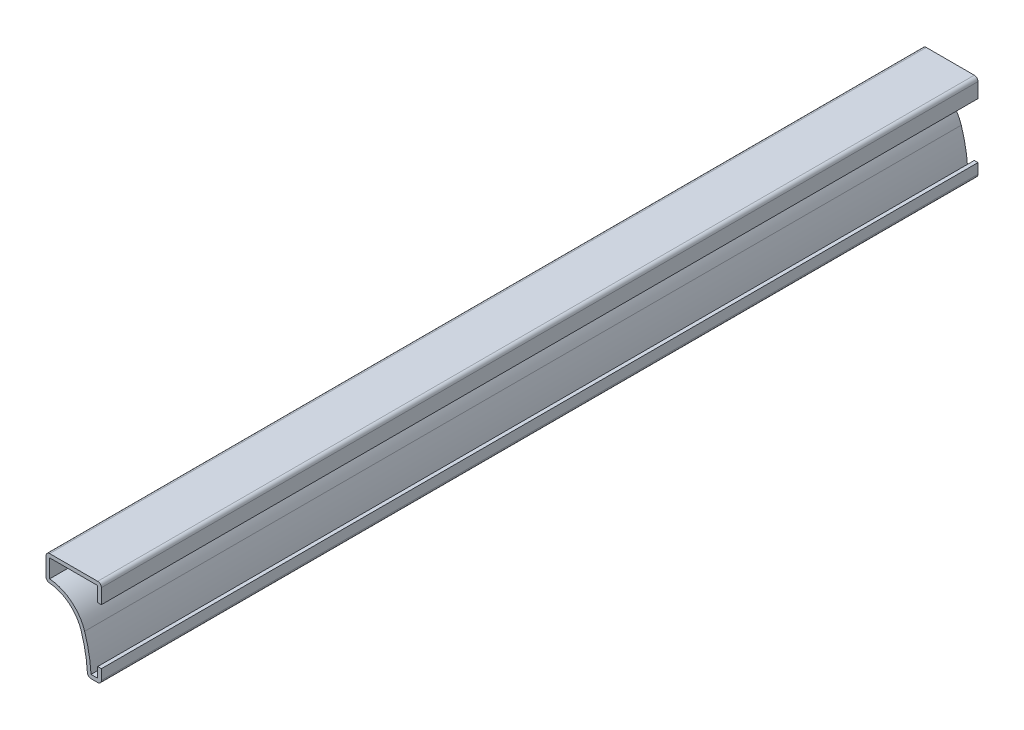
SolidWorks part; units mm, degrees
ref_plane "Front Plane" through (0, 0, 0) normal (0, 0, 1) x (1, 0, 0)
ref_plane "Top Plane" through (0, 0, 0) normal (0, 1, 0) x (1, 0, 0)
ref_plane "Right Plane" through (0, 0, 0) normal (1, 0, 0) x (0, 0, -1)
sketch "Sketch1" plane through (0, 0, 0) normal (0, 0, 1) x (1, 0, 0)
  line L0 (0, 0) -> (0, 6.35)
  line L1 (0, 6.35) -> (-19.05, 6.35)
  line L2 (-19.05, 6.35) -> (-19.05, -2.3813)
  line L3 (-4.7625, -23.8125) -> (0, -23.8125)
  line L4 (0, -23.8125) -> (0, -19.05)
  arc A0 (-19.05, -2.3813) -> (-6.9642, -11.1795) centre (-19.05, -15.0813) cw
  arc A1 (-6.9642, -11.1795) -> (-4.7625, -23.8125) centre (-50.7752, -25.3233) cw
extrude "Extrude-Thin1" add sketch "Sketch1" against normal blind 301.625 thin thin type one direction reverse wall 1.27
fillet "Fillet1" radius 1.27 5 edges at (0, -23.8125, -150.8125) (-4.7625, -23.8125, -150.8125) (-19.05, -2.3813, -150.8125) (-19.05, 6.35, -150.8125) (0, 6.35, -150.8125)
equation "\"D1@Extrude-Thin1\"=\"D1@Sketch1\"*10"
